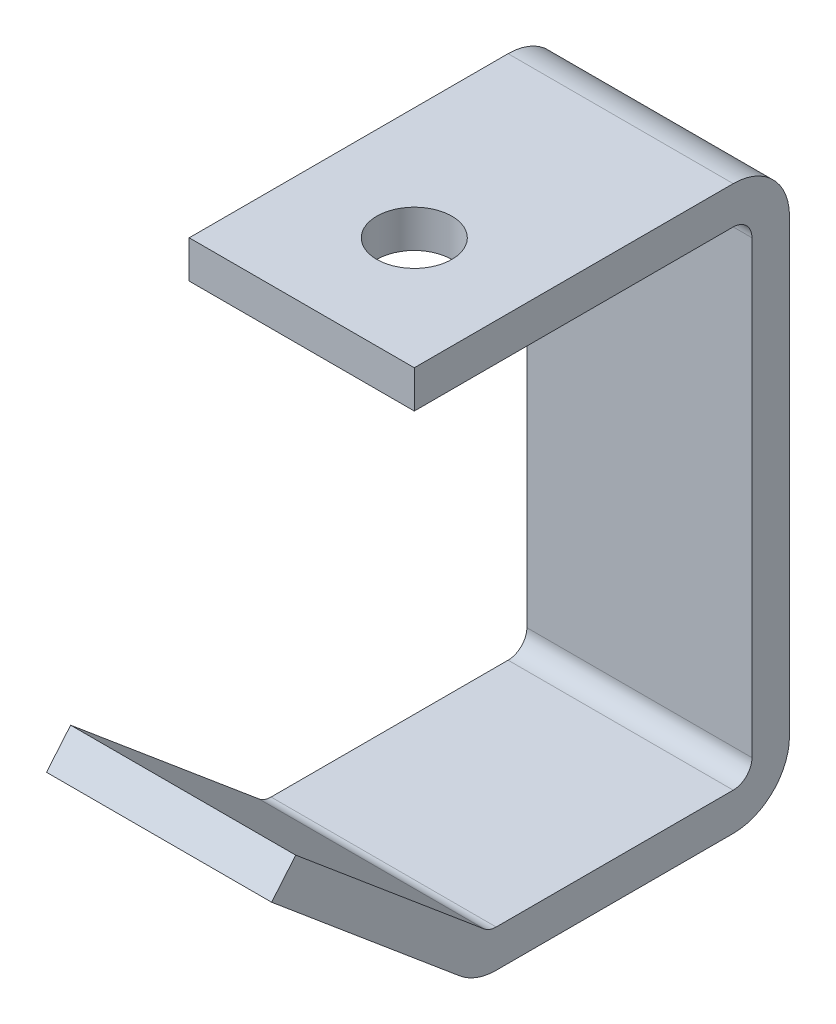
SolidWorks part; units mm, degrees
material "Alloy Steel"
ref_plane "Front Plane" through (0, 0, 0) normal (0, 0, 1) x (1, 0, 0)
ref_plane "Top Plane" through (0, 0, 0) normal (0, 1, 0) x (1, 0, 0)
ref_plane "Right Plane" through (0, 0, 0) normal (1, 0, 0) x (0, 0, -1)
sketch "Sketch1" plane through (0, 0, 0) normal (1, 0, 0) x (0, 0, -1)
  line L0 (0, 0) -> (0, 82.55)
  line L1 (0, 82.55) -> (-57.15, 82.55)
  line L2 (0, 0) -> (-44.45, 0)
  line L3 (-44.45, 0) -> (-77.2165, 27.4943)
  dimension "D1" = 57.15
  dimension "D2" = 82.55
  dimension "D3" = 44.45
  dimension "D4" = 42.7736
  dimension "D5" = 40
extrude "Extrude-Thin1" add sketch "Sketch1" along normal mid plane 38.1 thin
sketch "Sketch2" plane through (0, 88.9, 0) normal (0, 1, 0) x (1, 0, 0)
  circle A0 centre (0, -38.1) radius 6.35
  dimension "D1" = 12.7
  dimension "D2" = 19.05
extrude "Cut-Extrude1" cut sketch "Sketch2" against normal up to next
